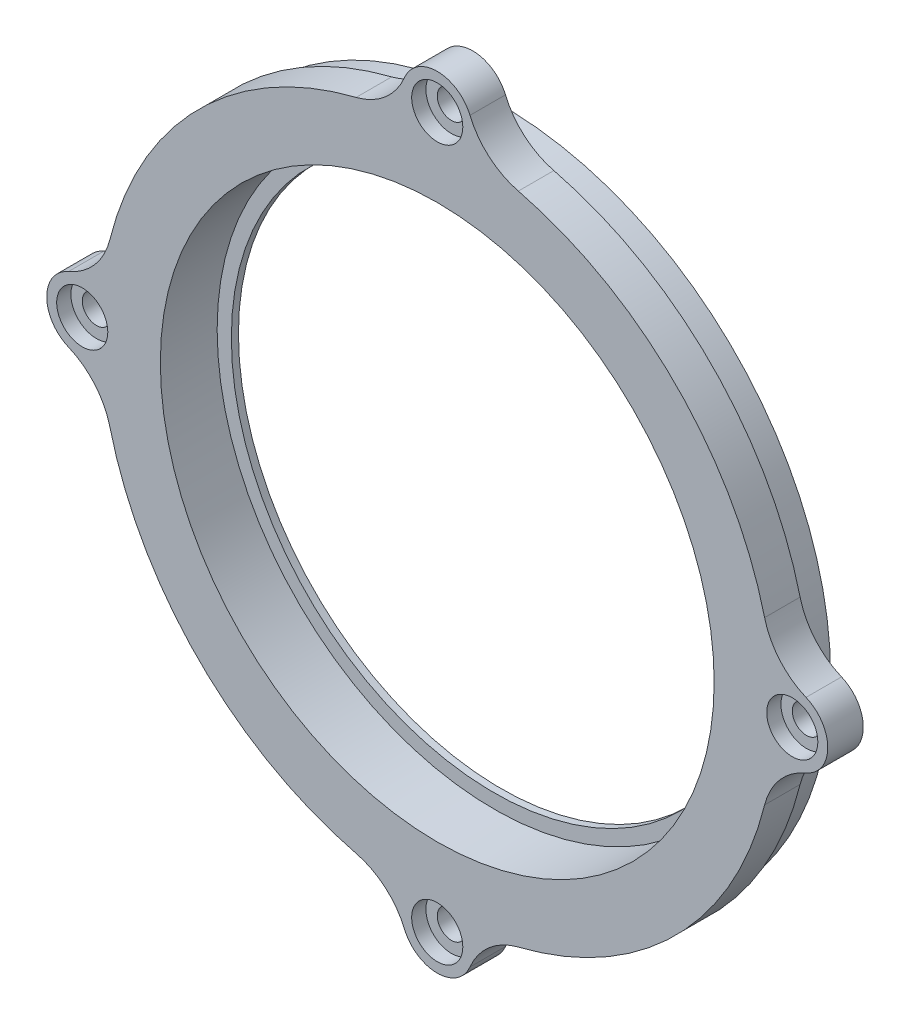
SolidWorks part; units mm, degrees
material "PET"
ref_plane "Front Plane" through (0, 0, 0) normal (0, 0, 1) x (1, 0, 0)
ref_plane "Top Plane" through (0, 0, 0) normal (0, 1, 0) x (1, 0, 0)
ref_plane "Right Plane" through (0, 0, 0) normal (1, 0, 0) x (0, 0, -1)
sketch "Sketch2" plane through (0, 0, 0) normal (0, 0, 1) x (1, 0, 0)
  circle A3 centre (0, 0) radius 50
  circle A4 centre (0, 0) radius 39
  dimension "D2" = 78
  dimension "D1" = 100
extrude "Boss-Extrude1" add sketch "Sketch2" along normal blind 5
sketch "Sketch3" plane through (0, 0, 0) normal (0, 0, -1) x (-1, 0, 0)
  circle A0 centre (-43, 0) radius 3
  circle A1 centre (0, 0) radius 39
  circle A2 centre (0, 0) radius 47
  circle A3 centre (0, 0) radius 50 construction
  circle A4 centre (-32.9399, 27.6399) radius 3
  circle A5 centre (-7.4669, 42.3467) radius 3
  circle A6 centre (21.5, 37.2391) radius 3
  circle A7 centre (40.4068, 14.7069) radius 3
  circle A8 centre (40.4068, -14.7069) radius 3
  circle A9 centre (21.5, -37.2391) radius 3
  circle A10 centre (-7.4669, -42.3467) radius 3
  circle A11 centre (-32.9399, -27.6399) radius 3
  point P27 (0, 0)
  dimension "D1" = 43
  dimension "D2" = 6
  dimension "D3" = 3
  dimension "D4" = 9
extrude "Boss-Extrude2" add sketch "Sketch3" along normal blind 4
sketch "Sketch4" plane through (0, 0, -4) normal (0, 0, -1) x (-1, 0, 0)
  circle A0 centre (0, 0) radius 39
  circle A1 centre (0, 0) radius 37
  dimension "D1" = 2
extrude "Boss-Extrude3" add sketch "Sketch4" against normal blind 1
sketch "Sketch6" plane through (0, 0, 5) normal (0, 0, 1) x (1, 0, 0)
  line L0 (0, 0) -> (52, 0) construction
  line L1 (0, 0) -> (0, 52) construction
  circle A0 centre (52, 0) radius 2
  circle A1 centre (52, 0) radius 5
  circle A2 centre (-52, 0) radius 5
  circle A3 centre (-52, 0) radius 2
  circle A4 centre (0, 52) radius 5
  circle A5 centre (0, 52) radius 2
  circle A8 centre (0, -52) radius 2
  circle A9 centre (0, -52) radius 5
  dimension "D1" = 4
  dimension "D4" = 10
  dimension "D5" = 4
  dimension "D3" = 52
  dimension "D6" = 52
  dimension "D2" = 3
extrude "Boss-Extrude4" add sketch "Sketch6" against normal up to surface (5 mm away) up to face at (-47, 0, 0)
fillet "Fillet1" radius 5 8 edges at (49.7981, -4.489, 2.5) (49.7981, 4.489, 2.5) (4.489, 49.7981, 2.5) (-4.489, 49.7981, 2.5) (-49.7981, 4.489, 2.5) (-49.7981, -4.489, 2.5) (-4.489, -49.7981, 2.5) (4.489, -49.7981, 2.5)
sketch "Sketch7" plane through (0, 0, 5) normal (0, 0, 1) x (1, 0, 0)
  circle A0 centre (52, 0) radius 3.6
  circle A1 centre (0, 52) radius 3.6
  circle A2 centre (-52, 0) radius 3.6
  circle A3 centre (0, -52) radius 3.6
  dimension "D1" = 7.2
  dimension "D2" = 7.2
  dimension "D3" = 7.2
  dimension "D4" = 7.2
extrude "Cut-Extrude1" cut sketch "Sketch7" against normal blind 3
sketch "Sketch8" plane through (0, 0, -4) normal (0, 0, -1) x (-1, 0, 0)
  circle A1 centre (-32.9399, 27.6399) radius 3.15
  circle A2 centre (-43, 0) radius 3.15
  circle A3 centre (-43, 0) radius 3.15
  circle A4 centre (-7.4669, 42.3467) radius 3.15
  circle A5 centre (21.5, 37.2391) radius 3.15
  circle A6 centre (40.4068, 14.7069) radius 3.15
  circle A7 centre (40.4068, -14.7069) radius 3.15
  circle A8 centre (21.5, -37.2391) radius 3.15
  circle A9 centre (-7.4669, -42.3467) radius 3.15
  circle A10 centre (-32.9399, -27.6399) radius 3.15
  point P22 (0, 0)
  dimension "D1" = 0.15
  dimension "D2" = 9
extrude "Cut-Extrude2" cut sketch "Sketch8" against normal up to surface (4 mm away) up to face at (29.9399, 27.6399, 0)
sketch "Sketch9" plane through (0, 0, -4) normal (0, 0, -1) x (-1, 0, 0)
  circle A0 centre (-43, 0) radius 3.15
  circle A1 centre (-32.9399, 27.6399) radius 3.15
  circle A2 centre (-7.4669, 42.3467) radius 3.15
  circle A3 centre (21.5, 37.2391) radius 3.15
  circle A4 centre (40.4068, 14.7069) radius 3.15
  circle A5 centre (40.4068, -14.7069) radius 3.15
  circle A6 centre (21.5, -37.2391) radius 3.15
  circle A7 centre (-7.4669, -42.3467) radius 3.15
  circle A8 centre (-32.9399, -27.6399) radius 3.15
  point P22 (0, 0)
  dimension "D1" = 9
extrude "Cut-Extrude3" cut sketch "Sketch9" against normal blind 6.6
sketch "Sketch10" plane through (0, 0, 0) normal (0, 0, -1) x (-1, 0, 0)
  circle A0 centre (0, 0) radius 47.5
  circle A1 centre (0, 0) radius 57.5
  dimension "D1" = 10
extrude "Cut-Extrude4" cut sketch "Sketch10" against normal up to surface (5 mm away) up to face at (55.6, 0, 5)
sketch "Sketch11" plane through (0, 0, -4) normal (0, 0, -1) x (-1, 0, 0)
  circle A2 centre (0, 0) radius 46.4
  circle A3 centre (0, 0) radius 46.4
  circle A5 centre (0, 0) radius 47.5
  circle A6 centre (0, 0) radius 47.5
  dimension "D1" = 1.1
  dimension "D2" = 0
extrude "Cut-Extrude5" cut sketch "Sketch11" against normal blind 4
sketch "Sketch12" plane through (0, 0, 5) normal (0, 0, 1) x (1, 0, 0)
  line L0 (0, 0) -> (50, 0) construction
  line L1 (0, 0) -> (50, 0) construction
  circle A1 centre (50, 0) radius 2
  circle A2 centre (0, -50) radius 2
  circle A3 centre (-50, 0) radius 2
  circle A4 centre (0, 50) radius 2
  circle A5 centre (50, 0) radius 5
  circle A6 centre (0, -50) radius 5
  circle A7 centre (-50, 0) radius 5
  circle A8 centre (0, 50) radius 5
  point P15 (0, 0)
  point P22 (0, 0)
  circle M5 centre (0, 0) radius 47.5
  dimension "D1" = 10
  dimension "D3" = 4
  dimension "D2" = 0
  dimension "D4" = 50
  dimension "D5" = 4
  dimension "D6" = 4
extrude "Boss-Extrude7" add sketch "Sketch12" against normal up to surface (5 mm away) contours A5 A1 M5 | A8 A4 M5 | A7 A3 M5 | A6 A2 M5
fillet "Fillet3" radius 10 8 edges at (4.2163, -47.3125, 2.5) (-4.2163, -47.3125, 2.5) (-47.3125, -4.2163, 2.5) (-47.3125, 4.2163, 2.5) (-4.2163, 47.3125, 2.5) (4.2163, 47.3125, 2.5) (47.3125, 4.2163, 2.5) (47.3125, -4.2163, 2.5)
sketch "Sketch14" plane through (0, 0, 5) normal (0, 0, 1) x (1, 0, 0)
  circle A0 centre (50, 0) radius 3.6
  circle A1 centre (0, -50) radius 3.6
  circle A2 centre (-50, 0) radius 3.6
  circle A3 centre (0, 50) radius 3.6
  point P12 (0, 0)
  dimension "D1" = 7.2
  dimension "D2" = 4
extrude "Cut-Extrude8" cut sketch "Sketch14" against normal blind 2
